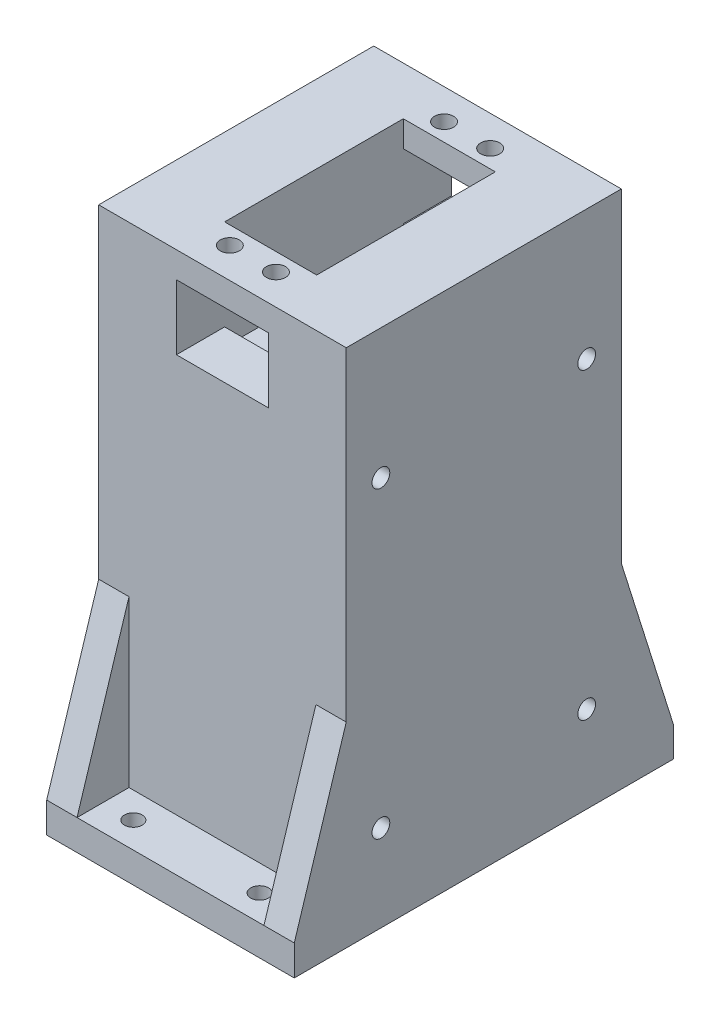
SolidWorks part; units mm, degrees
ref_plane "Front Plane" through (0, 0, 0) normal (0, 0, 1) x (1, 0, 0)
ref_plane "Top Plane" through (0, 0, 0) normal (0, 1, 0) x (1, 0, 0)
ref_plane "Right Plane" through (0, 0, 0) normal (1, 0, 0) x (0, 0, -1)
sketch "Sketch1" plane through (0, 0, 0) normal (0, 1, 0) x (1, 0, 0)
  line L1 (-28.575, -31.75) -> (28.575, -31.75)
  line L2 (-28.575, -31.75) -> (-28.575, 31.75)
  line L3 (-28.575, 31.75) -> (28.575, 31.75)
  line L4 (28.575, -31.75) -> (28.575, 31.75)
  line L5 (-28.575, -31.75) -> (28.575, 31.75) construction
  line L6 (-28.575, 31.75) -> (28.575, -31.75) construction
  point P0 (0, 0)
  dimension "D1" = 57.15
  dimension "D2" = 63.5
extrude "Boss-Extrude1" add sketch "Sketch1" along normal blind 120
sketch "Sketch2" plane through (0, 120, 0) normal (0, 1, 0) x (1, 0, 0)
  line L1 (-10.625, -20.625) -> (10.625, -20.625)
  line L2 (-10.625, -20.625) -> (-10.625, 20.625)
  line L3 (-10.625, 20.625) -> (10.625, 20.625)
  line L4 (10.625, -20.625) -> (10.625, 20.625)
  line L5 (-10.625, -20.625) -> (10.625, 20.625) construction
  line L6 (-10.625, 20.625) -> (10.625, -20.625) construction
  point P1 (0, 0)
  dimension "D1" = 21.25
  dimension "D2" = 41.25
extrude "Cut-Extrude1" cut sketch "Sketch2" against normal blind 25
sketch "Sketch3" plane through (0, 120, 0) normal (0, 1, 0) x (1, 0, 0)
  line L0 (0, 20.625) -> (0, 30.75) construction
  line L1 (10.625, 20.625) -> (-10.625, 20.625) construction
  line L2 (0, 30.75) -> (0, 25.6875) construction
  line L3 (10.625, -20.625) -> (10.625, 20.625) construction
  line L4 (10.625, 20.625) -> (-10.625, 20.625) construction
  line L5 (0, 0) -> (-2.4059, 0) construction
  circle A0 centre (5.325, 24.725) radius 2.2
  circle A1 centre (-5.325, 24.725) radius 2.2
  circle A2 centre (5.325, -24.725) radius 2.2
  circle A3 centre (-5.325, -24.725) radius 2.2
  dimension "D1" = 4.4
  dimension "D3" = 5.3
  dimension "D2" = 4.1
extrude "Cut-Extrude2" cut sketch "Sketch3" against normal blind 10
sketch "Sketch4" plane through (0, 0, 31.75) normal (0, 0, 1) x (1, 0, 0)
  line L0 (28.575, 120) -> (28.575, 0) construction
  line L1 (0, 120) -> (28.575, 120) construction
  line L2 (-28.575, 120) -> (-28.575, 95) construction
  line L3 (0, 95) -> (28.575, 95) construction
  line L4 (28.575, 120) -> (28.575, 95) construction
  line L5 (0, 120) -> (0, 99) construction
  line L6 (-28.575, 95) -> (0, 95) construction
  line L7 (-10.625, 99) -> (10.625, 99)
  line L8 (-10.625, 99) -> (-10.625, 114)
  line L9 (-10.625, 114) -> (10.625, 114)
  line L10 (10.625, 99) -> (10.625, 114)
  line L11 (-10.625, 99) -> (10.625, 114) construction
  line L12 (-10.625, 114) -> (10.625, 99) construction
  line L13 (0, 99) -> (0, 95) construction
  line L14 (-28.575, 120) -> (0, 120) construction
  point P9 (0, 106.5)
  dimension "D1" = 25
  dimension "D2" = 21.25
  dimension "D3" = 15
  dimension "D4" = 6
extrude "Cut-Extrude3" cut sketch "Sketch4" against normal through all
sketch "Sketch7" plane through (-28.575, 0, 0) normal (-1, 0, 0) x (0, 0, 1)
  line L0 (-31.75, 20) -> (31.75, 20) construction
  line L1 (-31.75, 120) -> (-31.75, 0) construction
  line L2 (31.75, 120) -> (31.75, 0) construction
  line L3 (-31.75, 90) -> (31.75, 90) construction
  line L4 (-31.75, 0) -> (31.75, 0) construction
  line L5 (0, 20) -> (0, 29.1745) construction
  circle A0 centre (23.75, 20) radius 2.05
  circle A1 centre (23.75, 90) radius 2.05
  circle A2 centre (-23.75, 20) radius 2.05
  circle A3 centre (-23.75, 90) radius 2.05
  dimension "D3" = 4.1
  dimension "D4" = 4.1
  dimension "D1" = 20
  dimension "D2" = 90
  dimension "D5" = 8
  dimension "D6" = 8
extrude "Cut-Extrude4" cut sketch "Sketch7" against normal through all
sketch "Sketch9" plane through (28.575, 0, 0) normal (1, 0, 0) x (0, 0, -1)
  line L0 (31.75, 120) -> (31.75, 0) construction
  line L1 (31.75, 7) -> (43.75, 7)
  line L2 (31.75, 7) -> (31.75, 0)
  line L3 (31.75, 0) -> (43.75, 0)
  line L4 (43.75, 7) -> (43.75, 0)
  line L5 (0, 0) -> (0, 30.2957) construction
  line L6 (-31.75, 0) -> (31.75, 0) construction
  line L7 (-31.75, 0) -> (-43.75, 0)
  line L8 (-43.75, 7) -> (-43.75, 0)
  line L9 (-31.75, 7) -> (-43.75, 7)
  line L10 (-31.75, 7) -> (-31.75, 0)
  dimension "D1" = 12
  dimension "D2" = 7
extrude "Boss-Extrude2" add sketch "Sketch9" against normal blind 57.15
sketch "Sketch10" plane through (0, 7, 0) normal (0, 1, 0) x (1, 0, 0)
  line L0 (-28.575, 37.75) -> (28.575, 37.75) construction
  line L1 (-28.575, 43.75) -> (-28.575, 31.75) construction
  line L2 (28.575, 43.75) -> (28.575, 31.75) construction
  line L3 (28.575, 0) -> (-28.575, 0) construction
  line L4 (28.575, -31.75) -> (28.575, 31.75) construction
  line L5 (-28.575, 31.75) -> (-28.575, -31.75) construction
  circle A0 centre (-14.575, 37.75) radius 2.05
  circle A1 centre (14.575, 37.75) radius 2.05
  circle A2 centre (14.575, -37.75) radius 2.05
  circle A3 centre (-14.575, -37.75) radius 2.05
  dimension "D1" = 4.1
  dimension "D2" = 4.1
  dimension "D3" = 14
  dimension "D4" = 14
extrude "Cut-Extrude5" cut sketch "Sketch10" against normal through all
sketch "Sketch11" plane through (28.575, 0, 0) normal (1, 0, 0) x (0, 0, -1)
  line L0 (-31.75, 45.1576) -> (-43.75, 7)
  line L1 (-31.75, 120) -> (-31.75, 7) construction
  line L2 (-43.75, 7) -> (-31.75, 7)
  line L3 (-31.75, 7) -> (-31.75, 45.1576)
  line L4 (0, 0) -> (0, 22.9689) construction
  line L5 (43.75, 7) -> (31.75, 7)
  line L6 (31.75, 45.1576) -> (43.75, 7)
  line L7 (31.75, 7) -> (31.75, 45.1576)
  dimension "D1" = 40
extrude "Boss-Extrude3" add sketch "Sketch11" against normal blind 7
sketch "Sketch12" plane through (-28.575, 0, 0) normal (-1, 0, 0) x (0, 0, 1)
  line L0 (-31.75, 45.1576) -> (-43.75, 7)
  line L1 (-43.75, 7) -> (-31.75, 7)
  line L2 (-31.75, 7) -> (-31.75, 45.1576)
  line L3 (0, 0) -> (0, 19.4079) construction
  line L4 (43.75, 7) -> (31.75, 7)
  line L5 (31.75, 45.1576) -> (43.75, 7)
  line L6 (31.75, 7) -> (31.75, 45.1576)
extrude "Boss-Extrude4" add sketch "Sketch12" against normal blind 7
sketch "Sketch13" plane through (0, 95, 0) normal (0, 1, 0) x (1, 0, 0)
  line L5 (-10.625, -10) -> (10.625, -10)
  line L6 (-10.625, -10) -> (-10.625, 10)
  line L7 (-10.625, 10) -> (10.625, 10)
  line L8 (10.625, -10) -> (10.625, 10)
  line L9 (-10.625, -10) -> (10.625, 10) construction
  line L10 (-10.625, 10) -> (10.625, -10) construction
  point P0 (0, 0)
  dimension "D1" = 20
  dimension "D2" = 21.25
extrude "Cut-Extrude6" cut sketch "Sketch13" against normal blind 60
